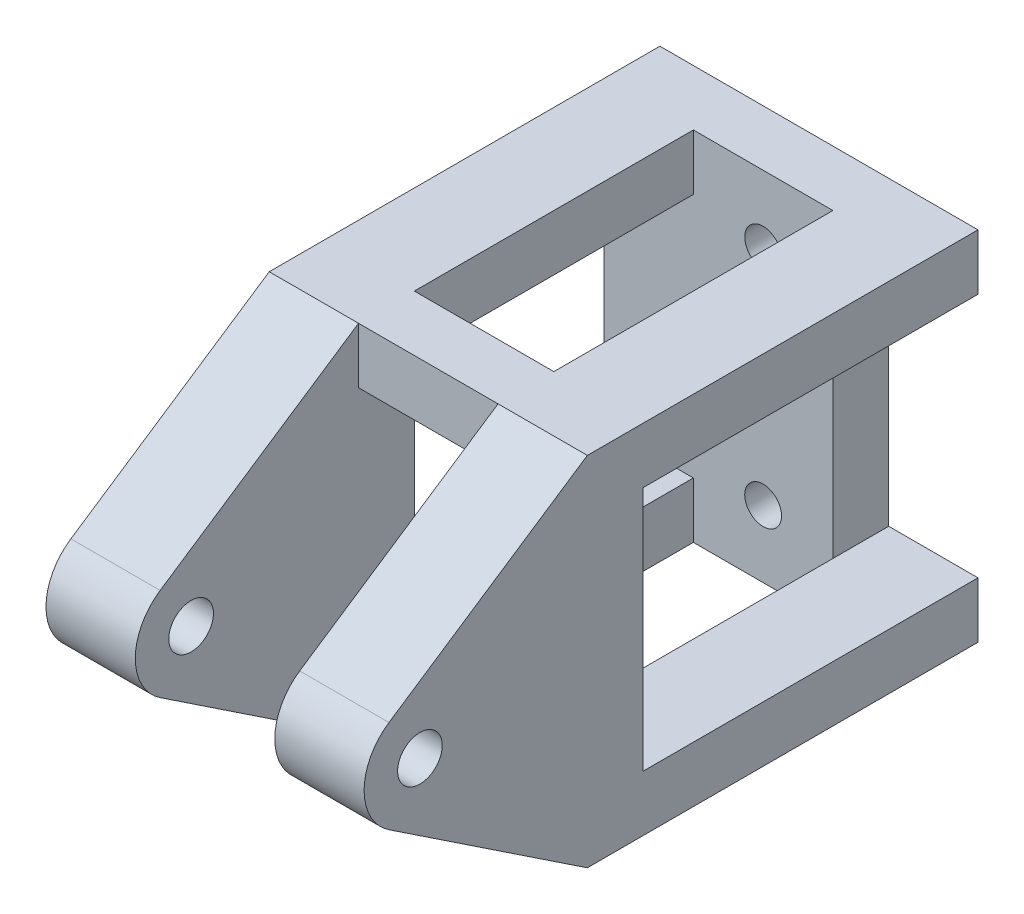
SolidWorks part; units mm, degrees
ref_plane "正面(Front)" through (0, 0, 0) normal (0, 0, 1) x (1, 0, 0)
ref_plane "平面(Top)" through (0, 0, 0) normal (0, 1, 0) x (1, 0, 0)
ref_plane "右側面(Right)" through (0, 0, 0) normal (1, 0, 0) x (0, 0, -1)
sketch "ｽｹｯﾁ1" plane through (0, 0, 0) normal (0, 0, 1) x (1, 0, 0)
  line L1 (-14.25, 16) -> (14.25, 16)
  line L2 (-14.25, 16) -> (-14.25, -16)
  line L3 (-14.25, -16) -> (14.25, -16)
  line L4 (14.25, 16) -> (14.25, -16)
  line L5 (-14.25, 16) -> (14.25, -16) construction
  line L6 (-14.25, -16) -> (14.25, 16) construction
  point P0 (0, 0)
  dimension "D1" = 28.5
  dimension "D2" = 32
extrude "ﾎﾞｽ - 押し出し1" add sketch "ｽｹｯﾁ1" along normal blind 5
sketch "ｽｹｯﾁ3" plane through (14.25, 0, 0) normal (1, 0, 0) x (0, 0, -1)
  line L0 (-5, 16) -> (-35, 16)
  line L1 (-35, 16) -> (-52.772, 4.1613)
  line L2 (0, 0) -> (-92.7849, 0) construction
  line L3 (-5, -16) -> (-5, 16) construction
  line L4 (-35, -16) -> (-52.772, -4.1613)
  line L5 (-5, -16) -> (-35, -16)
  line L6 (-5, -16) -> (-5, 16)
  arc A0 (-52.772, 4.1613) -> (-52.772, -4.1613) centre (-50, 0) ccw
  circle A1 centre (-50, 0) radius 2
  dimension "D2" = 5
  dimension "D4" = 4
  dimension "D1" = 45
  dimension "D3" = 30
extrude "ﾎﾞｽ - 押し出し2" add sketch "ｽｹｯﾁ3" against normal blind 8
mirror "ﾐﾗｰ1" about plane through (0, 0, 0) normal (1, 0, 0) of "ﾎﾞｽ - 押し出し2"
sketch "ｽｹｯﾁ4" plane through (0, 0, 5) normal (0, 0, 1) x (1, 0, 0)
  line L0 (0, 0) -> (26.7416, 0) construction
  line L1 (0, 0) -> (0, 23.9443) construction
  circle A0 centre (0, 10) radius 1.65
  circle A1 centre (0, -10) radius 1.65
  circle A2 centre (0, 10) radius 1.75 construction
  dimension "D1" = 3.3
extrude "ｶｯﾄ - 押し出し1" cut sketch "ｽｹｯﾁ4" against normal through all
sketch "ｽｹｯﾁ5" plane through (0, 0, 0) normal (0, 0, 1) x (1, 0, 0)
  circle A0 centre (12.35, -5) radius 1.75 construction
  circle A1 centre (12.35, -5) radius 1.75 construction
  circle A2 centre (12.35, 5) radius 1.75 construction
  circle A3 centre (12.35, 5) radius 1.75 construction
  circle A4 centre (12.35, -5) radius 1.65
  circle A5 centre (12.35, 5) radius 1.65
  dimension "D1" = 3.3
extrude "ｶｯﾄ - 押し出し2" cut sketch "ｽｹｯﾁ5" along normal blind 5
sketch "ｽｹｯﾁ6" plane through (14.25, 0, 0) normal (1, 0, 0) x (0, 0, -1)
  line L0 (0, 0) -> (-33.2812, 0) construction
  line L1 (-35, 16) -> (0, 16) construction
  line L2 (-30, 11) -> (-5, 11)
  line L3 (-30, 11) -> (-30, -11)
  line L4 (-30, -11) -> (-5, -11)
  line L5 (-5, 11) -> (-5, -11)
  line L6 (-30, 11) -> (-5, -11) construction
  line L7 (-30, -11) -> (-5, 11) construction
  point P3 (-17.5, 0)
  dimension "D1" = 5
  dimension "D2" = 5
  dimension "D3" = 25
extrude "ｶｯﾄ - 押し出し3" cut sketch "ｽｹｯﾁ6" against normal through all
sketch "ｽｹｯﾁ7" plane through (-6.25, 0, 0) normal (1, 0, 0) x (0, 0, -1)
  line L0 (-5, 11) -> (-30, 11) construction
  line L1 (-35, 16) -> (-30, 16)
  line L2 (-35, 16) -> (-35, 11)
  line L3 (-35, 11) -> (-30, 11)
  line L4 (-30, 16) -> (-30, 11)
  line L5 (-30, 11) -> (-30, -11) construction
  line L6 (0, 0) -> (-57.9494, 0) construction
  line L7 (-35, -16) -> (-30, -16)
  line L8 (-35, -16) -> (-35, -11)
  line L9 (-35, -11) -> (-30, -11)
  line L10 (-30, -16) -> (-30, -11)
extrude "ﾎﾞｽ - 押し出し3" add sketch "ｽｹｯﾁ7" along normal up to next
sketch "ｽｹｯﾁ8" plane through (0, 0, 0) normal (0, 0, -1) x (-1, 0, 0)
  line L0 (-14.25, -16) -> (-14.25, 16) construction
  line L1 (-14.25, -11) -> (-6.25, -11)
  line L2 (-14.25, -11) -> (-14.25, 11)
  line L3 (-14.25, 11) -> (-6.25, 11)
  line L4 (-6.25, -11) -> (-6.25, 11)
  dimension "D1" = 8
extrude "ｶｯﾄ - 押し出し4" cut sketch "ｽｹｯﾁ8" against normal blind 10
